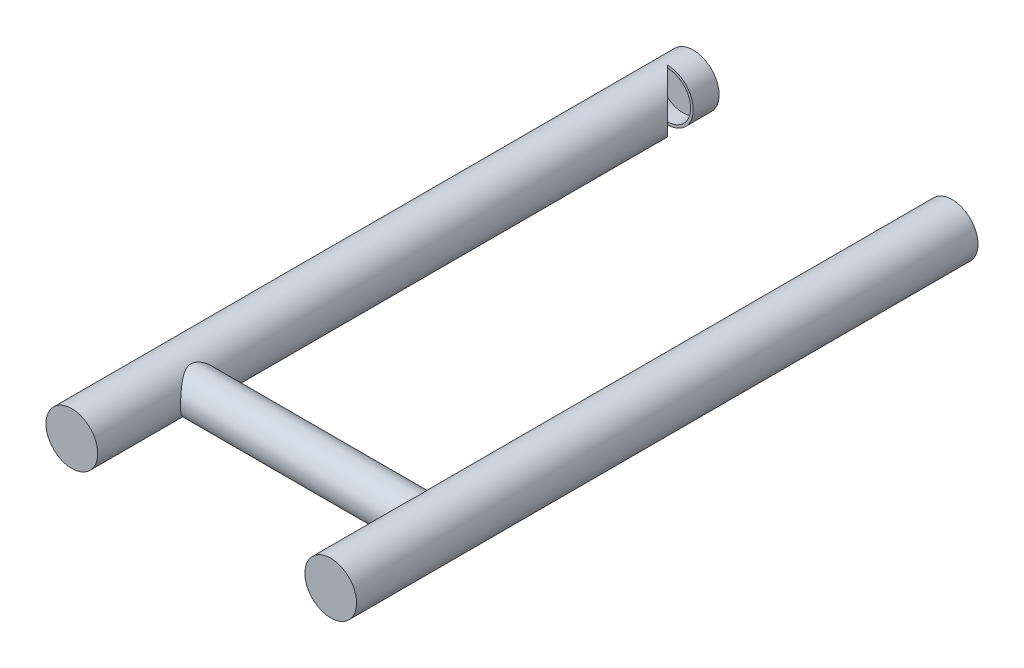
SolidWorks part; units mm, degrees
ref_plane "Front Plane" through (0, 0, 0) normal (0, 0, 1) x (1, 0, 0)
ref_plane "Top Plane" through (0, 0, 0) normal (0, 1, 0) x (1, 0, 0)
ref_plane "Right Plane" through (0, 0, 0) normal (1, 0, 0) x (0, 0, -1)
sketch "Sketch1" plane through (0, 0, 0) normal (0, 0, 1) x (1, 0, 0)
  circle A0 centre (0, 0) radius 12.7
  circle A1 centre (127, 0) radius 12.7
  dimension "D1" = 25.4
  dimension "D2" = 25.4
  dimension "D3" = 127
extrude "Boss-Extrude2" add sketch "Sketch1" along normal blind 304.8
sketch "Sketch3" plane through (0, 0, 0) normal (0, 1, 0) x (1, 0, 0)
  line L0 (0, 5.8713) -> (0, -351.43) construction
  line L1 (12.7, -12.7) -> (0, -12.7)
  line L2 (12.7, -304.8) -> (12.7, 0) construction
  line L3 (0, -12.7) -> (12.7, -25.4)
  line L4 (12.7, -25.4) -> (12.7, -12.7)
  dimension "D1" = 45
  dimension "D2" = 12.7
  dimension "D3" = 12.7
sketch "Sketch10" plane through (0, 0, 0) normal (0, 0, -1) x (-1, 0, 0)
  circle A0 centre (0, 0) radius 11.43
  dimension "D1" = 22.86
extrude "Cut-Extrude1" cut sketch "Sketch10" against normal up to surface (304.8 mm away) up to face at (12.7, 0, 304.8)
sketch "Sketch11" plane through (0, 0, 0) normal (0, 0, -1) x (-1, 0, 0)
  circle A0 centre (0, 0) radius 11.43 construction
  circle A1 centre (0, 0) radius 11.43
extrude "Boss-Extrude3" add sketch "Sketch11" against normal blind 5.08
sketch "Sketch12" plane through (0, 0, 304.8) normal (0, 0, 1) x (1, 0, 0)
  circle A0 centre (0, 0) radius 11.43 construction
  circle A1 centre (0, 0) radius 11.43
extrude "Boss-Extrude4" add sketch "Sketch12" against normal blind 5.08
extrude "Cut-Extrude2" cut sketch "Sketch3" against normal mid plane 27.94 contours L1 L3 L4
sketch "Sketch14" plane through (0, 0, 0) normal (0, 0, -1) x (-1, 0, 0)
  circle A0 centre (-127, 0) radius 11.43
  point P0 (-127, 0)
  dimension "D1" = 22.86
extrude "Cut-Extrude3" cut sketch "Sketch14" against normal blind 299.72
ref_plane "Plane2" through (63.5, 0, 0) normal (1, 0, 0) x (0, 0, -1)
sketch "Sketch15" plane through (63.5, 0, 0) normal (1, 0, 0) x (0, 0, -1)
  line L0 (-304.8, 12.7) -> (-304.8, -12.7) construction
  circle A0 centre (-254, 0) radius 10.16
  dimension "D1" = 20.32
  dimension "D2" = 50.8
extrude "Boss-Extrude5" add sketch "Sketch15" along normal up to next and the other way up to next
sketch "Sketch17" plane through (0, 0, 0) normal (1, 0, 0) x (0, 0, -1)
  line L0 (-304.8, 12.7) -> (-304.8, -12.7) construction
  circle A0 centre (-254, 0) radius 8.89
  dimension "D2" = 17.78
  dimension "D1" = 50.8
extrude "Cut-Extrude4" cut sketch "Sketch17" along normal up to next
